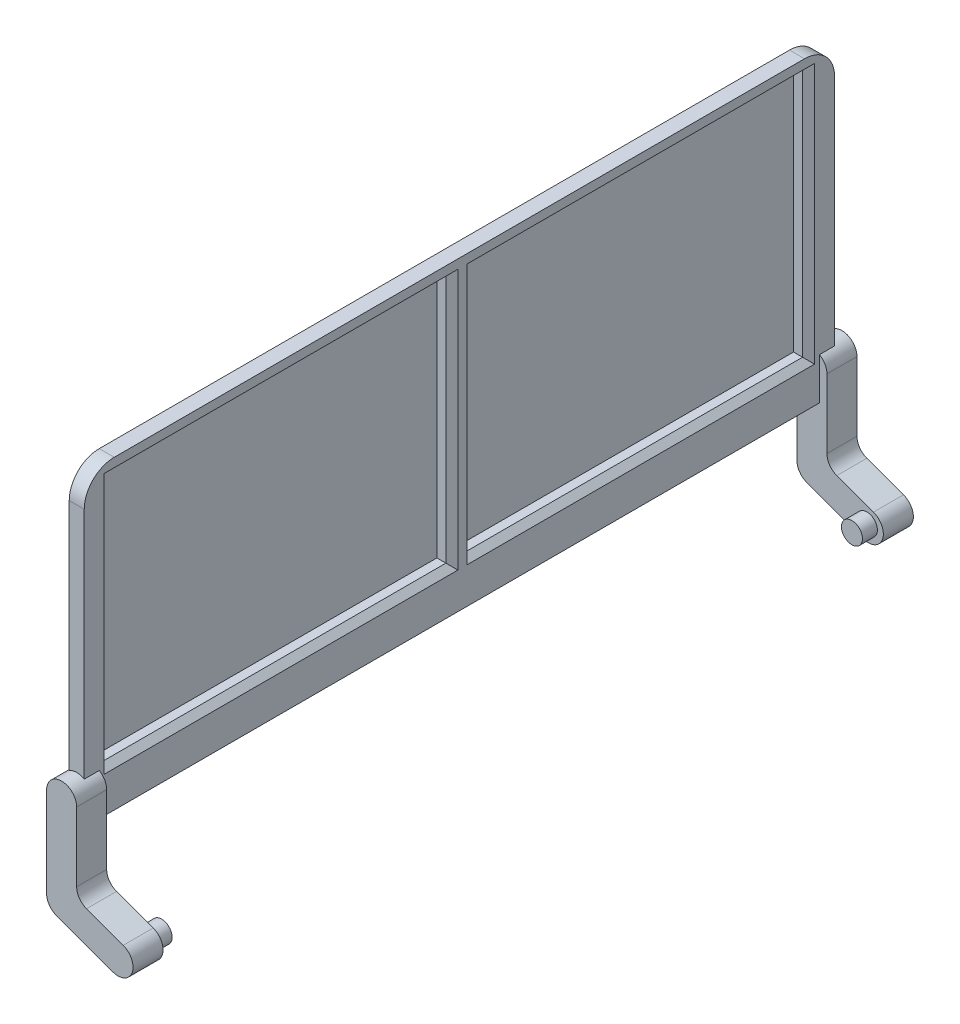
SolidWorks part; units mm, degrees
ref_plane "Front Plane" through (0, 0, 0) normal (0, 0, 1) x (1, 0, 0)
ref_plane "Top Plane" through (0, 0, 0) normal (0, 1, 0) x (1, 0, 0)
ref_plane "Right Plane" through (0, 0, 0) normal (1, 0, 0) x (0, 0, -1)
sketch "Sketch1" plane through (0, 0, 0) normal (1, 0, 0) x (0, 0, -1)
  line L0 (0, 0) -> (0, 101.8) construction
  line L1 (-115, 101.8) -> (115, 101.8)
  line L2 (-125, 91.8) -> (-125, 0)
  line L3 (-125, 0) -> (125, 0)
  line L4 (125, 91.8) -> (125, 0)
  line L5 (116.3397, 14) -> (2.5, 14)
  line L6 (-116.3397, 96.8) -> (-2.5, 96.8)
  line L7 (-116.3397, 96.8) -> (-116.3397, 14)
  line L8 (-116.3397, 14) -> (-2.5, 14)
  line L9 (-2.5, 96.8) -> (-2.5, 14)
  line L10 (116.3397, 96.8) -> (116.3397, 14)
  line L11 (116.3397, 96.8) -> (2.5, 96.8)
  line L12 (2.5, 96.8) -> (2.5, 14)
  arc A0 (115, 101.8) -> (125, 91.8) centre (115, 91.8) cw
  arc A1 (-125, 91.8) -> (-115, 101.8) centre (-115, 91.8) cw
  point P17 (125, 101.8)
  point P20 (-125, 101.8)
  dimension "D8" = 10
  dimension "D1" = 250
  dimension "D2" = 101.8
  dimension "D3" = 5
  dimension "D4" = 14
  dimension "D5" = 10
  dimension "D6" = 125
  dimension "D7" = 5
extrude "Boss-Extrude1" add sketch "Sketch1" along normal blind 5
chamfer "Chamfer1" distance 2 angle 45 7 edges at (5, 96.8, -59.4199) (5, 55.4, -116.3397) (5, 14, -59.4199) (5, 55.4, 116.3397) (5, 96.8, 59.4199) (5, 55.4, 2.5) (5, 14, 59.4199)
sketch "Sketch2" plane through (0, 0, 125) normal (0, 0, 1) x (1, 0, 0)
  line L0 (0, 0) -> (5, 0)
  line L1 (5, 0) -> (0, 0.8816)
  line L2 (0, 91.8) -> (0, 0) construction
  line L3 (0, 0.8816) -> (0, 0)
  dimension "D1" = 10
extrude "Boss-Extrude2" add sketch "Sketch2" against normal through all
sketch "Sketch3" plane through (0, 0, 125) normal (0, 0, 1) x (1, 0, 0)
  line L0 (2.4719, 9.6) -> (2.4719, -20.4) construction
  line L3 (2.4719, -20.4) -> (21.2658, -27.2404) construction
  line L5 (-2.5281, 9.6) -> (-2.5281, -20.4)
  line L6 (0.7618, -25.0985) -> (19.5557, -31.9389)
  line L7 (7.4719, 9.6) -> (7.4719, -13.3979)
  line L8 (10.7618, -18.0964) -> (22.9759, -22.5419)
  line L9 (-2.5281, -23.901) -> (19.5557, -31.9389) construction
  line L10 (-2.5281, 9.6) -> (-2.5281, -23.901) construction
  line L11 (7.4719, -16.899) -> (22.9759, -22.5419) construction
  line L12 (7.4719, 9.6) -> (7.4719, -16.899) construction
  arc A0 (-2.5281, 9.6) -> (7.4719, 9.6) centre (2.4719, 9.6) cw
  arc A1 (19.5557, -31.9389) -> (22.9759, -22.5419) centre (21.2658, -27.2404) ccw
  arc A2 (0.7618, -25.0985) -> (-2.5281, -20.4) centre (2.4719, -20.4) cw
  arc A3 (10.7618, -18.0964) -> (7.4719, -13.3979) centre (12.4719, -13.3979) cw
  dimension "D7" = 5
  dimension "D1" = 30
  dimension "D2" = 20
  dimension "D3" = 92.2
  dimension "D4" = 110
  dimension "D5" = 5
  dimension "D6" = 5
extrude "Boss-Extrude5" add sketch "Sketch3" along normal mid plane 10
sketch "Sketch4" plane through (0, 0, 120) normal (0, 0, -1) x (-1, 0, 0)
  line L5 (-0.7618, -25.0985) -> (-19.5557, -31.9389) construction
  circle A0 centre (-20.7959, -27.0694) radius 3.5
  arc A2 (-22.9759, -22.5419) -> (-19.5557, -31.9389) centre (-21.2658, -27.2404) ccw construction
  dimension "D1" = 7
  dimension "D2" = 5
  dimension "D3" = 0.5
extrude "Boss-Extrude6" add sketch "Sketch4" along normal blind 5
ref_plane "Plane1" through (0, 0, 0) normal (0, 0, 1) x (1, 0, 0)
mirror "Mirror13" about plane through (0, 0, 0) normal (0, 0, 1) of "Boss-Extrude5", "Boss-Extrude6"
sketch "Sketch8" plane through (0, 0, 0) normal (-1, 0, 0) x (0, 0, 1)
  line L4 (116.3397, 96.8) -> (2.5, 96.8)
  line L5 (116.3397, 14) -> (116.3397, 96.8)
  line L6 (2.5, 14) -> (116.3397, 14)
  line L7 (2.5, 96.8) -> (2.5, 14)
  line L8 (116.3397, 96.8) -> (2.5, 96.8)
  line L9 (116.3397, 14) -> (116.3397, 96.8)
  line L10 (2.5, 14) -> (116.3397, 14)
  line L11 (2.5, 96.8) -> (2.5, 14)
  line L12 (-116.3397, 14) -> (-2.5, 14)
  line L13 (-116.3397, 96.8) -> (-116.3397, 14)
  line L14 (-2.5, 96.8) -> (-116.3397, 96.8)
  line L15 (-2.5, 14) -> (-2.5, 96.8)
  line L16 (-116.3397, 14) -> (-2.5, 14)
  line L17 (-116.3397, 96.8) -> (-116.3397, 14)
  line L18 (-2.5, 96.8) -> (-116.3397, 96.8)
  line L19 (-2.5, 14) -> (-2.5, 96.8)
  dimension "D1" = 0
  dimension "D2" = 0
extrude "Boss-Extrude8" add sketch "Sketch8" along normal blind 1 separate body
